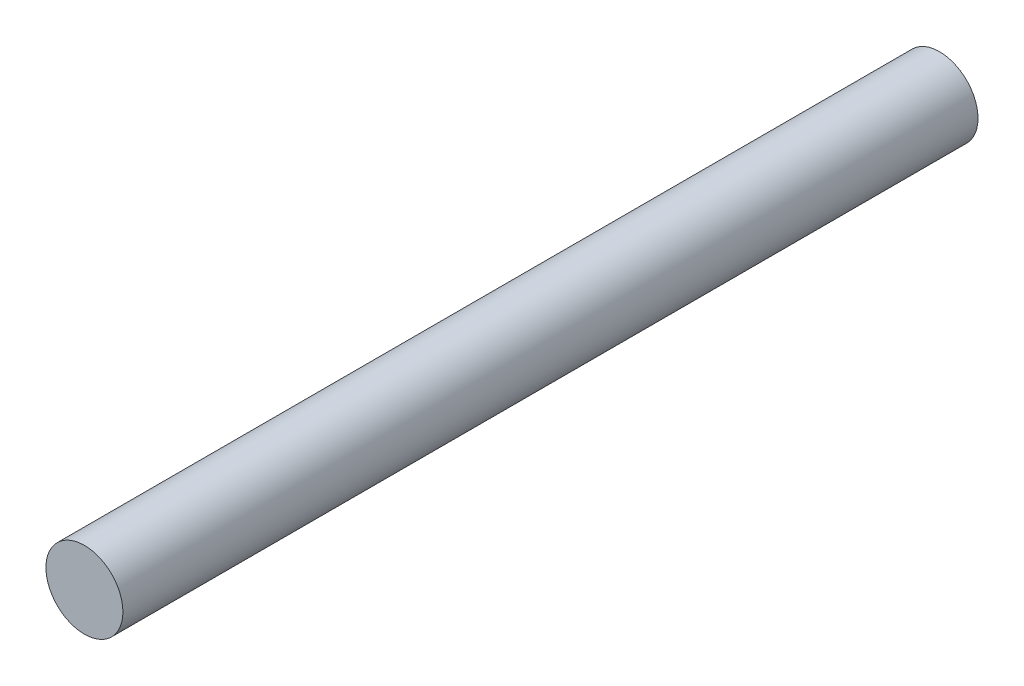
SolidWorks part; units mm, degrees
ref_plane "Front Plane" through (0, 0, 0) normal (0, 0, 1) x (1, 0, 0)
ref_plane "Top Plane" through (0, 0, 0) normal (0, 1, 0) x (1, 0, 0)
ref_plane "Right Plane" through (0, 0, 0) normal (1, 0, 0) x (0, 0, -1)
surface "Surface-Offset1" parameters "D1"=0
ref_plane "Plane1" through (0, 0, 179.1665) normal (0, 0, 1) x (1, 0, 0)
ref_plane "Plane2" through (0, 0, 108.6358) normal (0, 0, 1) x (1, 0, 0)
sketch "Sketch2" plane through (0, 0, 179.1665) normal (0, 0, 1) x (1, 0, 0)
  circle A0 centre (-336.55, 927.1) radius 3.175 construction
  circle A1 centre (-336.55, 927.1) radius 3.175
extrude "Boss-Extrude1" add sketch "Sketch2" against normal up to surface (70.5307 mm away) up to plane "Plane2"
